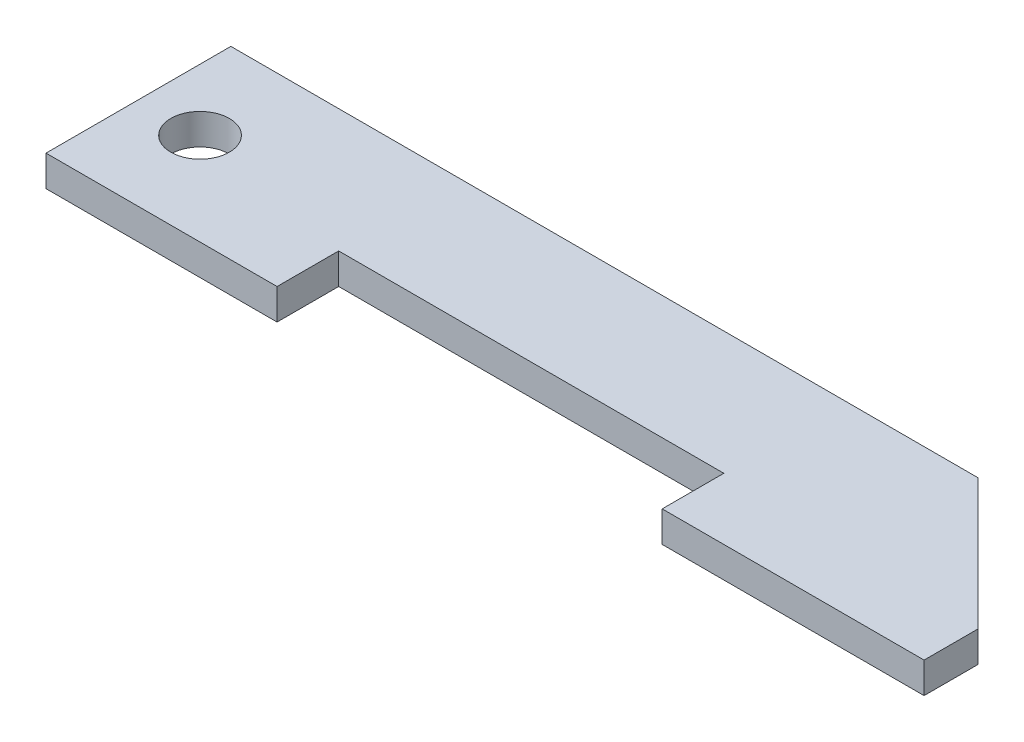
SolidWorks part; units mm, degrees
ref_plane "Спереди" through (0, 0, 0) normal (0, 0, 1) x (1, 0, 0)
ref_plane "Сверху" through (0, 0, 0) normal (0, 1, 0) x (1, 0, 0)
ref_plane "Справа" through (0, 0, 0) normal (1, 0, 0) x (0, 0, -1)
sketch "Эскиз1" plane through (0, 0, 0) normal (0, 1, 0) x (1, 0, 0)
  line L0 (0, 0) -> (48.5, 0)
  line L1 (48.5, 0) -> (57, -8.5)
  line L3 (57, -8.5) -> (57, -12)
  line L4 (57, -12) -> (40, -12)
  line L5 (40, -12) -> (40, -8)
  line L6 (40, -8) -> (15, -8)
  line L7 (15, -8) -> (15, -12)
  line L8 (15, -12) -> (0, -12)
  line L9 (0, -12) -> (0, 0)
  circle A0 centre (4, -6) radius 1.9
  dimension "D7" = 3.8
  dimension "D8" = 6
  dimension "D1" = 25
  dimension "D2" = 12
  dimension "D3" = 45
  dimension "D4" = 3.5
  dimension "D5" = 57
  dimension "D6" = 17
  dimension "D9" = 11
  dimension "D10" = 4
extrude "Бобышка-Вытянуть1" add sketch "Эскиз1" along normal blind 2
